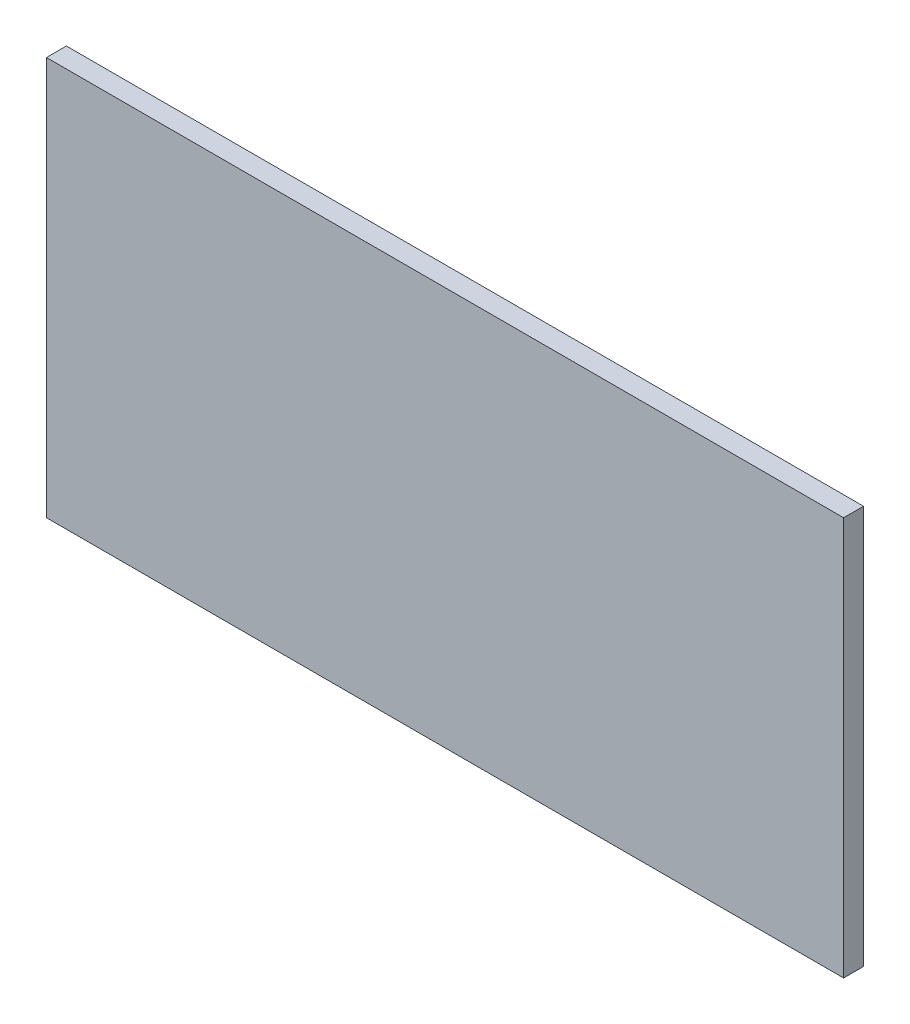
SolidWorks part; units mm, degrees
material "Oak"
ref_plane "Front Plane" through (0, 0, 0) normal (0, 0, 1) x (1, 0, 0)
ref_plane "Top Plane" through (0, 0, 0) normal (0, 1, 0) x (1, 0, 0)
ref_plane "Right Plane" through (0, 0, 0) normal (1, 0, 0) x (0, 0, -1)
sketch "Sketch1" plane through (0, 0, 0) normal (0, 0, 1) x (1, 0, 0)
  line L1 (0, 0) -> (400, 0)
  line L2 (0, 0) -> (0, 200)
  line L3 (0, 200) -> (400, 200)
  line L4 (400, 0) -> (400, 200)
  dimension "D1" = 200
  dimension "D2" = 400
extrude "Boss-Extrude1" add sketch "Sketch1" along normal blind 10
